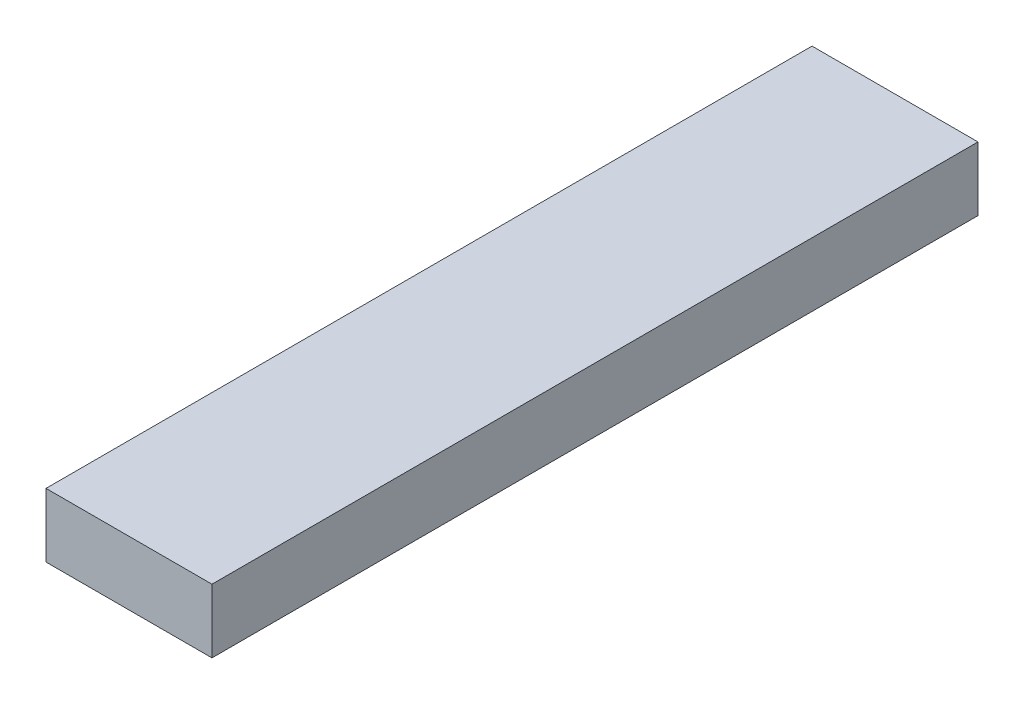
SolidWorks part; units mm, degrees
ref_plane "Plan de face" through (0, 0, 0) normal (0, 0, 1) x (1, 0, 0)
ref_plane "Plan de dessus" through (0, 0, 0) normal (0, 1, 0) x (1, 0, 0)
ref_plane "Plan de droite" through (0, 0, 0) normal (1, 0, 0) x (0, 0, -1)
sketch "Esquisse1" plane through (0, 0, 0) normal (0, 0, 1) x (1, 0, 0)
  line L1 (0, 0) -> (13, 0)
  line L2 (0, 0) -> (0, -5)
  line L3 (0, -5) -> (13, -5)
  line L4 (13, 0) -> (13, -5)
  dimension "D1" = 13
  dimension "D2" = 5
extrude "Boss.-Extru.1" add sketch "Esquisse1" along normal blind 60
